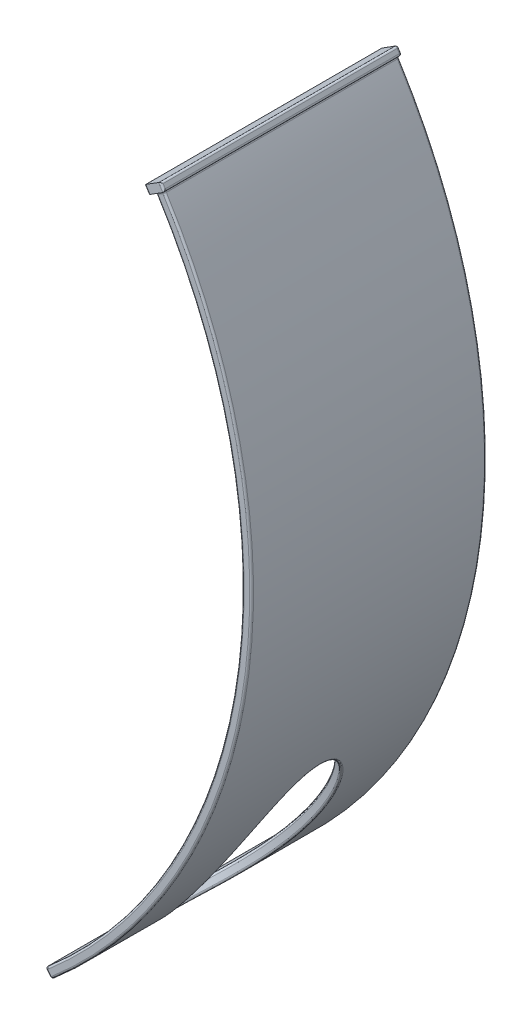
SolidWorks part; units mm, degrees
ref_plane "Front Plane" through (0, 0, 0) normal (0, 0, 1) x (1, 0, 0)
ref_plane "Top Plane" through (0, 0, 0) normal (0, 1, 0) x (1, 0, 0)
ref_plane "Right Plane" through (0, 0, 0) normal (1, 0, 0) x (0, 0, -1)
ref_plane "Plane1" through (-17.5, 0, 0) normal (1, 0, 0) x (0, 0, -1)
ref_plane "Plane2" through (-35, 0, 0) normal (1, 0, 0) x (0, 0, -1)
sketch "Sketch1" plane through (-17.5, 0, 0) normal (1, 0, 0) x (0, 0, -1)
  line L0 (0, 0) -> (0, -50) construction
  dimension "D1" = 50
sketch "Sketch2" plane through (0, 0, 0) normal (1, 0, 0) x (0, 0, -1)
  point P0 (0, 0)
sketch "Sketch3" plane through (-35, 0, 0) normal (1, 0, 0) x (0, 0, -1)
  point P0 (0, 0)
sketch "Sketch4" plane through (0, 0, 0) normal (0, 0, 1) x (1, 0, 0)
  line L0 (-17.5, 0) -> (-17.5, -50) construction
  arc A0 (9.9992, -0.126) -> (-45, -0.1273) centre (-17.5, -17.4818) cw construction
  arc A1 (9.9992, -0.126) -> (3.7287, -42.1146) centre (-17.5, -17.4818) cw construction
  dimension "D1" = 10
  dimension "D3" = 32.5182
  dimension "D4" = 46.2567
  dimension "D2" = 10
sketch "Sketch6" plane through (0, 0, 0) normal (0, 0, 1) x (1, 0, 0)
  line L0 (15.0182, 10) -> (15.0182, -39.6825) construction
  arc A0 (3.7287, -42.1146) -> (9.9992, -0.126) centre (-17.5, -17.4818) ccw construction
  dimension "D1" = 32.5182
ref_plane "Plane3" through (15.0182, 0, 0) normal (1, 0, 0) x (0, 0, -1)
sketch "Sketch7" plane through (0, 0, 0) normal (0, 0, 1) x (1, 0, 0)
  arc A0 (12.8322, 1.6619) -> (5.9157, -44.6523) centre (-17.5, -17.4818) cw
  dimension "D1" = 3.35
  dimension "D3" = 35.8682
  dimension "D2" = 3.35
sketch "Sketch8" plane through (0, 0, 0) normal (0, 0, 1) x (1, 0, 0)
  line L0 (18.3682, 1.0018) -> (18.3682, -40.6587) construction
  arc A0 (5.9157, -44.6523) -> (12.8322, 1.6619) centre (-17.5, -17.4818) ccw construction
ref_plane "Plane4" through (18.3682, 0, 0) normal (1, 0, 0) x (0, 0, -1)
sketch "Sketch10" plane through (18.3682, 0, 0) normal (1, 0, 0) x (0, 0, -1)
  line L0 (-26.4109, -17.4818) -> (24.946, -17.4818) construction
  dimension "D1" = 0
ref_plane "Plane5" through (0, -17.4818, 0) normal (0, 1, 0) x (1, 0, 0)
sketch "Sketch11" plane through (0, -17.4818, 0) normal (0, 1, 0) x (1, 0, 0)
  line L0 (18.3682, -26.4109) -> (18.3682, 24.946) construction
  line L1 (18.3682, 7.5) -> (18.9682, 7.5)
  line L2 (18.3682, 7.5) -> (18.3682, -7.5)
  line L3 (18.3682, -7.5) -> (18.9682, -7.5)
  line L4 (18.9682, 7.5) -> (18.9682, -7.5)
  line L5 (5.9157, 0) -> (18.3682, 0) construction
  dimension "D1" = 0.6
  dimension "D2" = 15
  dimension "D3" = 7.5
sweep "Sweep1" add profiles "Sketch11" path "Sketch7"
sketch "Sketch12" plane through (-18.687, -16.1046, 0) normal (-0.7575, -0.6528, 0) x (0, 0, 1)
  line L1 (-7.5, -37.6863) -> (7.5, -37.6863)
  line L2 (-7.5, -37.6863) -> (-7.5, -38.2863)
  line L3 (-7.5, -38.2863) -> (7.5, -38.2863)
  line L4 (7.5, -37.6863) -> (7.5, -38.2863)
extrude "Boss-Extrude1" add sketch "Sketch12" along normal blind 0.2
sketch "Sketch14" plane through (2.9053, -4.6033, 0) normal (-0.5337, 0.8457, 0) x (0.8457, 0.5337, 0)
  line L0 (12.3386, 7.5) -> (11.7386, 7.5) construction
  line L1 (12.6386, -7.7) -> (11.4386, -7.7)
  line L2 (12.6386, -7.7) -> (12.6386, 7.5)
  line L3 (12.6386, 7.5) -> (11.4386, 7.5)
  line L4 (11.4386, -7.7) -> (11.4386, 7.5)
  line L5 (12.3386, -7.5) -> (12.3386, 7.5) construction
  dimension "D1" = 1.2
  dimension "D2" = 15.2
  dimension "D3" = 0
  dimension "D4" = 0.3
extrude "Boss-Extrude2" add sketch "Sketch14" along normal blind 0.5
sketch "Sketch15" plane through (24.6026, -28.5477, 0) normal (-0.6528, 0.7575, 0) x (0.7575, 0.6528, 0)
  line L0 (-24.669, -7.5) -> (10.8054, -7.5) construction
  line L1 (-24.669, 7.5) -> (-24.669, -7.5) construction
  ellipse E0 centre (-16.669, 0) end of major axis (-24.1782, 0) minor radius 3.4038
  dimension "D1" = 7.5
  dimension "D2" = 8
extrude "Cut-Extrude1" cut sketch "Sketch15" against normal through all both and the other way through all
fillet "Fillet1" radius 0.12 28 edges at (5.7642, -44.7828, 0) (12.3116, 1.9246, 0.1) (12.445, 1.7132, 7.7) (12.5785, 1.5018, 0.1) (13.4598, 2.3537, 7.7) (13.3264, 2.5651, 0.1) (13.5932, 2.1423, 0.1) (5.8399, -44.7175, -7.5) (5.96, -45.0101, -7.5) (13.4664, 2.0622, -7.5) (13.4598, 2.3537, -7.5) (12.819, 2.2449, -7.5) (12.445, 1.7132, -7.5) (12.7053, 1.5819, -7.5) (5.96, -45.0101, 7.5) (5.8399, -44.7175, 7.5) (13.0859, 1.8221, 7.5) (6.2316, -45.172, -7.5) (6.1558, -45.2373, 0) (6.2316, -45.172, 7.5) (18.5682, -22.8682, 7.5) (13.3396, 1.9822, 0) (18.5682, -22.8682, -7.5) (17.9748, -22.7796, -7.5) (12.8322, 1.6619, 0) (17.9748, -22.7796, 7.5) (15.7891, -32.3736, -0.2094) (15.3107, -31.9727, -0.5931)
